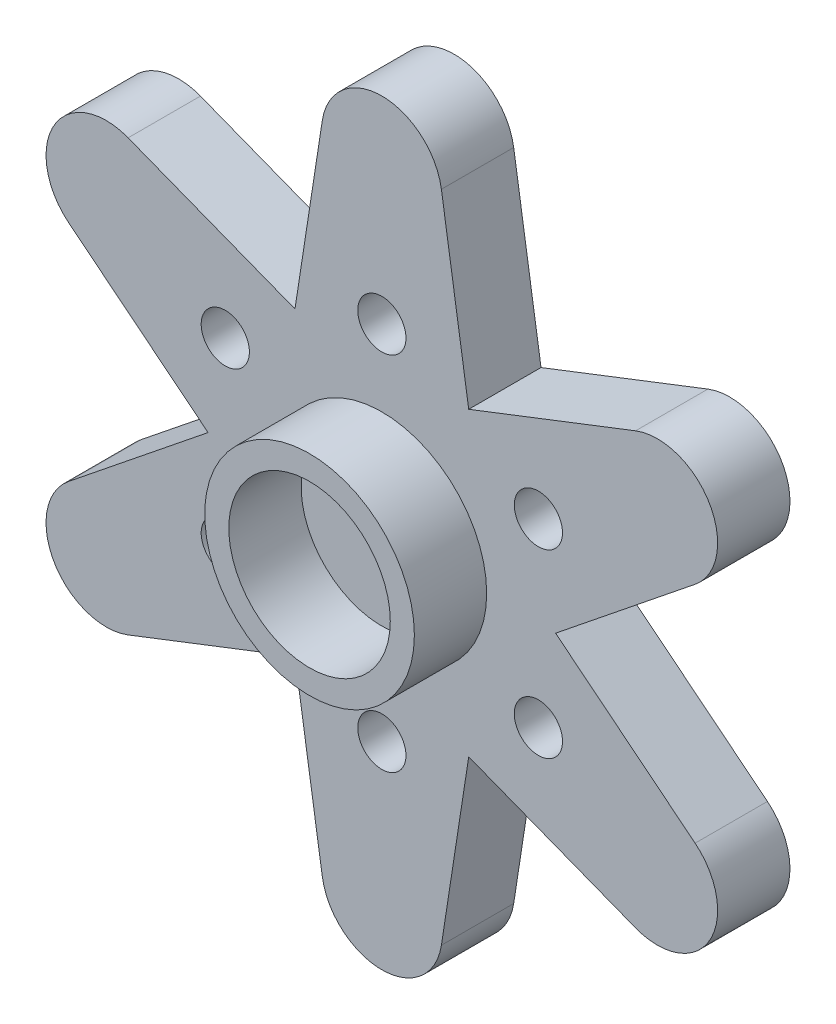
SolidWorks part; units mm, degrees
ref_plane "前视基准面" through (0, 0, 0) normal (0, 0, 1) x (1, 0, 0)
ref_plane "上视基准面" through (0, 0, 0) normal (0, 1, 0) x (1, 0, 0)
ref_plane "右视基准面" through (0, 0, 0) normal (1, 0, 0) x (0, 0, -1)
sketch "草图1" plane through (0, 0, 0) normal (0, 0, 1) x (1, 0, 0)
  line L0 (-2.4707, 13.5816) -> (-3.6043, 6.2428)
  line L1 (0, 29.2442) -> (0, 0) construction
  line L2 (2.4707, 13.5816) -> (3.6043, 6.2428)
  line L3 (10.5267, 8.9305) -> (3.6043, 6.2428)
  line L4 (12.9974, 4.6511) -> (7.2086, 0)
  line L5 (25.3262, 14.6221) -> (0, 0) construction
  line L6 (12.9974, -4.6511) -> (7.2086, 0)
  line L7 (10.5267, -8.9305) -> (3.6043, -6.2428)
  line L8 (25.3262, -14.6221) -> (0, 0) construction
  line L9 (2.4707, -13.5816) -> (3.6043, -6.2428)
  line L10 (-2.4707, -13.5816) -> (-3.6043, -6.2428)
  line L11 (0, -29.2442) -> (0, 0) construction
  line L12 (-10.5267, -8.9305) -> (-3.6043, -6.2428)
  line L13 (-12.9974, -4.6511) -> (-7.2086, 0)
  line L14 (-25.3262, -14.6221) -> (0, 0) construction
  line L15 (-12.9974, 4.6511) -> (-7.2086, 0)
  line L16 (-10.5267, 8.9305) -> (-3.6043, 6.2428)
  line L17 (-25.3262, 14.6221) -> (0, 0) construction
  arc A0 (12.9974, 4.6511) -> (10.5267, 8.9305) centre (11.4315, 6.6) ccw
  arc A1 (2.4707, 13.5816) -> (-2.4707, 13.5816) centre (0, 13.2) ccw
  circle A2 centre (6.4952, 3.75) radius 1
  arc A3 (10.5267, -8.9305) -> (12.9974, -4.6511) centre (11.4315, -6.6) ccw
  circle A4 centre (0, 7.5) radius 1
  circle A5 centre (6.4952, -3.75) radius 1
  arc A6 (-2.4707, -13.5816) -> (2.4707, -13.5816) centre (0, -13.2) ccw
  circle A7 centre (0, -7.5) radius 1
  arc A8 (-12.9974, -4.6511) -> (-10.5267, -8.9305) centre (-11.4315, -6.6) ccw
  circle A9 centre (-6.4952, -3.75) radius 1
  arc A10 (-10.5267, 8.9305) -> (-12.9974, 4.6511) centre (-11.4315, 6.6) ccw
  circle A11 centre (-6.4952, 3.75) radius 1
  point P18 (0, 0)
  point P20 (0, 0)
  point P22 (0, 0)
  point P25 (0, 0)
  point P31 (0, 0)
  point P33 (0, 0)
  point P41 (0, 0)
  point P43 (0, 0)
  point P51 (0, 0)
  point P53 (0, 0)
  point P61 (0, 0)
  point P63 (0, 0)
  point P64 (0, 0)
  dimension "D1" = 13.2
  dimension "D2" = 5
  dimension "D3" = 7.5
  dimension "D4" = 6
extrude "凸台-拉伸1" add sketch "草图1" along normal blind 3
sketch "草图2" plane through (0, 0, 3) normal (0, 0, 1) x (1, 0, 0)
  circle A0 centre (0, 0) radius 4.35
extrude "拉伸-薄壁1" add sketch "草图2" along normal offset from surface (3 mm away) 6 thin up to face at (-5.4952, -3.75, 0) thin type one direction reverse wall 1
